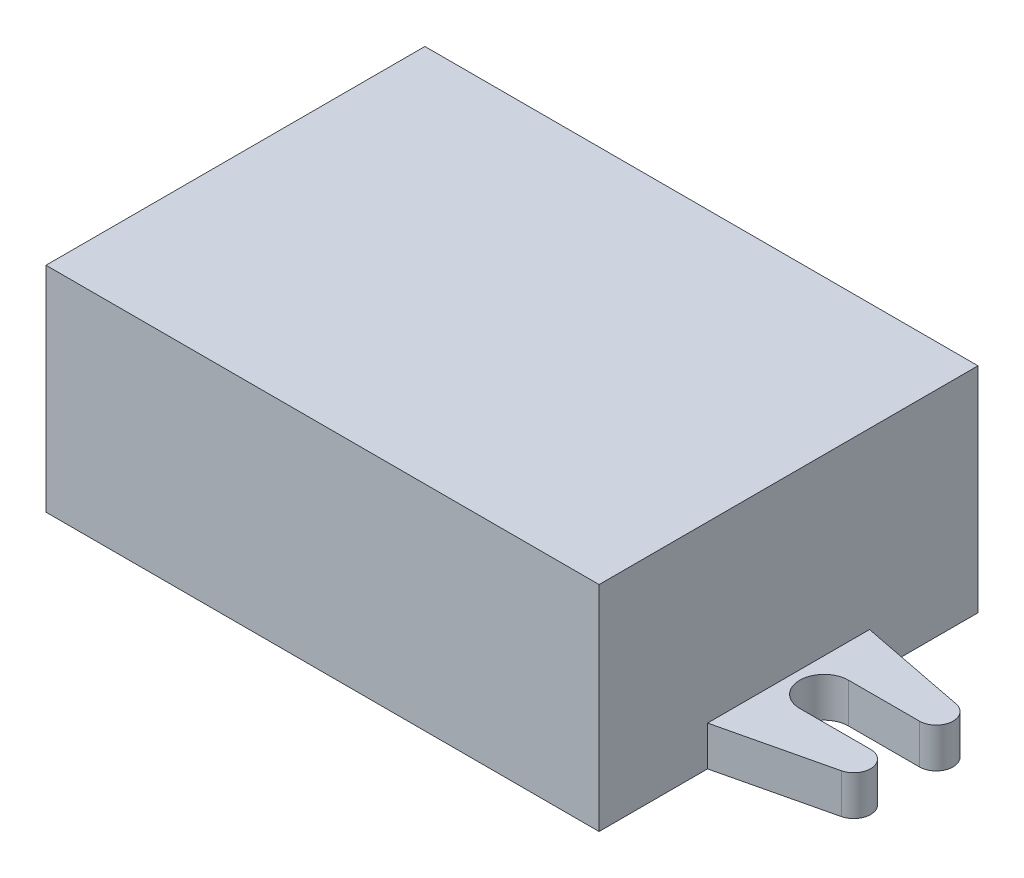
SolidWorks part; units mm, degrees
ref_plane "Front Plane" through (0, 0, 0) normal (0, 0, 1) x (1, 0, 0)
ref_plane "Top Plane" through (0, 0, 0) normal (0, 1, 0) x (1, 0, 0)
ref_plane "Right Plane" through (0, 0, 0) normal (1, 0, 0) x (0, 0, -1)
sketch "Sketch1" plane through (0, 0, 0) normal (0, 1, 0) x (1, 0, 0)
  line L1 (-21.7715, 15.5655) -> (24.2025, 15.5655)
  line L2 (-21.7715, 15.5655) -> (-21.7715, -15.9305)
  line L3 (-21.7715, -15.9305) -> (24.2025, -15.9305)
  line L4 (24.2025, 15.5655) -> (24.2025, -15.9305)
  dimension "D1" = 45.974
  dimension "D2" = 31.496
extrude "Boss-Extrude2" add sketch "Sketch1" along normal blind 17.78 contours L1 L4 L3 L2
sketch "Sketch2" plane through (0, 0, 0) normal (0, -1, 0) x (1, 0, 0)
  line L0 (-21.7715, 6.9135) -> (-21.7715, -6.5485)
  line L1 (-21.7715, -15.5655) -> (-21.7715, 15.9305) construction
  line L2 (-21.7715, -9.2565) -> (-29.6455, -9.2565)
  line L3 (-21.7715, -6.5485) -> (-30.8008, -4.7785)
  line L4 (-21.7715, 6.9135) -> (-30.7608, 4.7885)
  line L5 (-30.4395, -2.032) -> (-24.5466, -2.032)
  line L6 (-30.4395, 2.032) -> (-24.5466, 2.032)
  line L7 (1.2155, 15.9305) -> (1.2155, -15.5655)
  line L8 (-21.7715, 15.9305) -> (24.2025, 15.9305) construction
  line L9 (-21.7715, -15.5655) -> (24.2025, -15.5655) construction
  line L10 (32.8706, 2.032) -> (26.9777, 2.032)
  line L11 (32.8706, -2.032) -> (26.9777, -2.032)
  line L12 (24.2025, 6.9135) -> (33.1919, 4.7885)
  line L13 (24.2025, -6.5485) -> (33.2319, -4.7785)
  line L14 (24.2025, 6.9135) -> (24.2025, -6.5485)
  arc A0 (-24.5466, -2.032) -> (-24.5466, 2.032) centre (-24.5466, 0) ccw
  arc A1 (-30.7608, 4.7885) -> (-30.4395, 2.032) centre (-30.4395, 3.429) ccw
  arc A2 (-30.4395, -2.032) -> (-30.8008, -4.7785) centre (-30.4395, -3.429) ccw
  arc A3 (32.8706, -2.032) -> (33.2319, -4.7785) centre (32.8706, -3.429) cw
  arc A4 (33.1919, 4.7885) -> (32.8706, 2.032) centre (32.8706, 3.429) cw
  arc A5 (26.9777, -2.032) -> (26.9777, 2.032) centre (26.9777, 0) cw
  dimension "D3" = 7.874
  dimension "D4" = 3.429
  dimension "D1" = 9.017
  dimension "D2" = 13.462
  dimension "D5" = 3.429
extrude "Boss-Extrude6" add sketch "Sketch2" against normal blind 3.302 contours L0 L3 A2 L5 A0 L6 A1 L4 | L14 L13 A3 L11 A5 L10 A4 L12
sketch "Sketch3" plane through (0, 0, -15.5655) normal (0, 0, -1) x (-1, 0, 0)
  circle A0 centre (-18.7316, 4.9501) radius 2.1998
  circle A1 centre (16.8526, 4.9501) radius 2.0088
